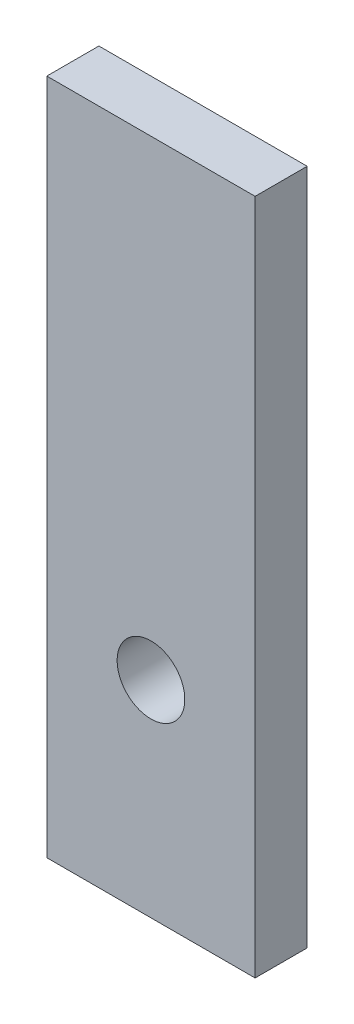
SolidWorks part; units mm, degrees
material "ABS"
ref_plane "Front Plane" through (0, 0, 0) normal (0, 0, 1) x (1, 0, 0)
ref_plane "Top Plane" through (0, 0, 0) normal (0, 1, 0) x (1, 0, 0)
ref_plane "Right Plane" through (0, 0, 0) normal (1, 0, 0) x (0, 0, -1)
sketch "Sketch1" plane through (0, 0, 0) normal (0, 0, 1) x (1, 0, 0)
  line L1 (-8.0879, -35.5054) -> (-3.0079, -35.5054)
  line L2 (-8.0879, -35.5054) -> (-8.0879, -18.9954)
  line L3 (-8.0879, -18.9954) -> (-3.0079, -18.9954)
  line L4 (-3.0079, -35.5054) -> (-3.0079, -18.9954)
  point P0 (0, 0)
  dimension "D1" = 16.51
  dimension "D2" = 5.08
extrude "Boss-Extrude1" add sketch "Sketch1" along normal blind 1.27
sketch "Sketch2" plane through (0, 0, 0) normal (0, 0, -1) x (-1, 0, 0)
  line L0 (5.5479, -18.9954) -> (5.5479, 49981.0046) construction
  line L1 (3.0079, -18.9954) -> (8.0879, -18.9954) construction
  line L2 (8.0879, -27.2504) -> (50008.0879, -27.2504) construction
  line L3 (8.0879, -18.9954) -> (8.0879, -35.5054) construction
  circle A0 centre (5.5479, -30.48) radius 0.8255
  point P4 (5.5479, -18.9954)
  point P9 (8.0879, -27.2504)
extrude "Cut-Extrude1" cut sketch "Sketch2" against normal blind 2.54
sketch "Sketch3" plane through (0, 0, 0) normal (0, 0, -1) x (-1, 0, 0)
  line L0 (5.5479, -18.9954) -> (5.5479, -35.5054) construction
  line L1 (3.0079, -18.9954) -> (8.0879, -18.9954) construction
  line L2 (8.0879, -35.5054) -> (3.0079, -35.5054) construction
  line L4 (8.0879, -18.9954) -> (8.0879, -35.5054) construction
  line L5 (8.0879, -30.48) -> (3.0079, -30.48) construction
  line L6 (3.0079, -35.5054) -> (3.0079, -18.9954) construction
